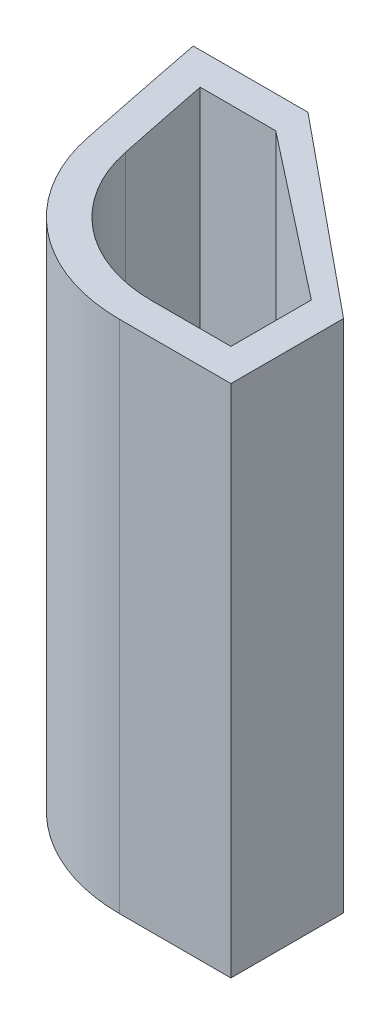
SolidWorks part; units mm, degrees
ref_plane "Front Plane" through (0, 0, 0) normal (0, 0, 1) x (1, 0, 0)
ref_plane "Top Plane" through (0, 0, 0) normal (0, 1, 0) x (1, 0, 0)
ref_plane "Right Plane" through (0, 0, 0) normal (1, 0, 0) x (0, 0, -1)
sketch "Sketch1" plane through (0, 0, 0) normal (0, 1, 0) x (1, 0, 0)
  line L4 (-1.7289, 4.41) -> (-5.2956, 4.41)
  line L5 (0.9191, -4.09) -> (4.3762, -4.09)
  line L6 (4.3762, -0.59) -> (4.3762, -4.09)
  line L9 (-1.7289, 3.41) -> (3.3762, -0.59)
  line L10 (-1.7289, 4.41) -> (4.3762, -0.59)
  line L15 (-1.7289, 3.41) -> (-4.0795, 3.41)
  line L16 (0.9191, -3.09) -> (3.3762, -3.09)
  line L17 (3.3762, -0.59) -> (3.3762, -3.09)
  arc A4 (-5.2956, 4.41) -> (-4.4659, 0.2908) centre (330.5168, 69.91) ccw
  arc A5 (-4.4659, 0.2908) -> (0.9191, -4.09) centre (0.9191, 1.41) ccw
  arc A9 (-4.0795, 3.41) -> (-3.4868, 0.4943) centre (330.5168, 69.91) ccw
  arc A10 (-3.4868, 0.4943) -> (0.9191, -3.09) centre (0.9191, 1.41) ccw
  point P0 (-4.7862, 4.41)
  point P1 (-3.9763, 0.3926)
  point P2 (330.5168, 69.91)
  point P3 (0.9191, -3.59)
  point P5 (4.3762, -3.59)
  point P8 (-5.3927, 4.91)
  point P14 (4.8762, -4.09)
extrude "Boss-Extrude1" add sketch "Sketch1" along normal blind 16
sketch "Sketch2" plane through (1.4676, 0, -1.792) normal (0.6336, 0, -0.7737) x (-0.7737, 0, -0.6336)
  line L0 (0.1862, 16) -> (0, 0) construction
  line L1 (-3.7595, 16) -> (4.1318, 16) construction
  line L2 (-3.7595, 8) -> (4.1318, 8) construction
  line L3 (-3.7595, 16) -> (-3.7595, 0) construction
  line L4 (4.1318, 16) -> (4.1318, 0) construction
  circle A0 centre (0.0931, 8) radius 1.6
  dimension "D1" = 3.2
extrude "Cut-Extrude1" cut sketch "Sketch2" against normal up to surface (0.7347 mm away)
